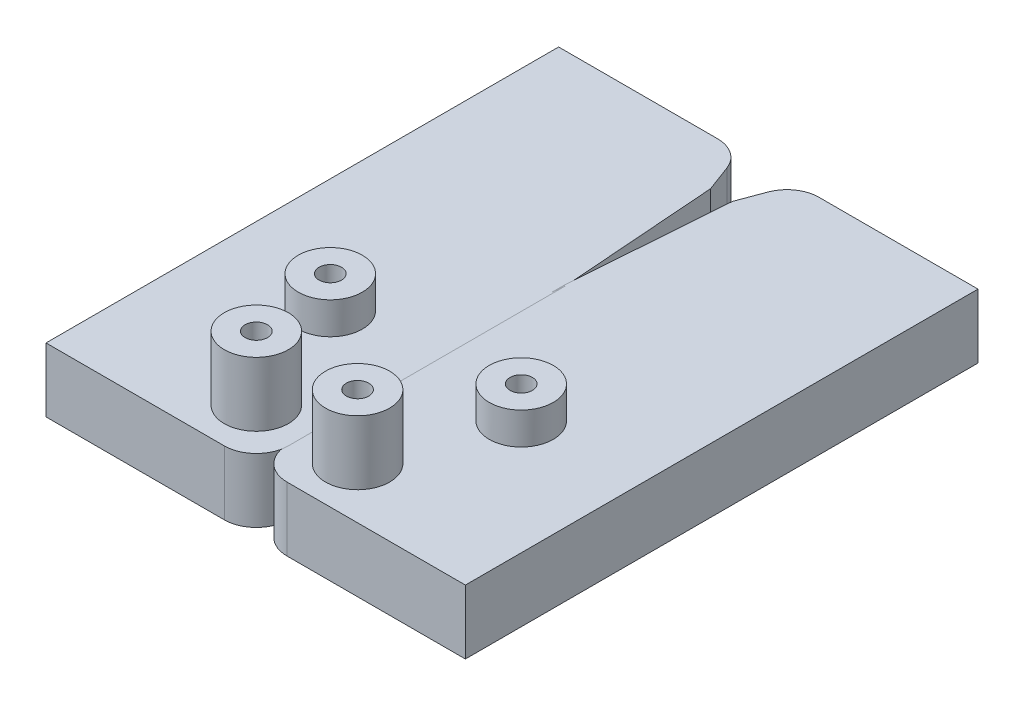
SolidWorks part; units mm, degrees
ref_plane "Front Plane" through (0, 0, 0) normal (0, 0, 1) x (1, 0, 0)
ref_plane "Top Plane" through (0, 0, 0) normal (0, 1, 0) x (1, 0, 0)
ref_plane "Right Plane" through (0, 0, 0) normal (1, 0, 0) x (0, 0, -1)
sketch "Sketch1" plane through (0, 0, 0) normal (0, 1, 0) x (1, 0, 0)
  line L0 (-32.7242, 27.6175) -> (-7.9076, 27.6175)
  line L1 (-3.2221, 24.3628) -> (-1.7139, 20.314)
  line L2 (-1.7139, 20.314) -> (0.1, -4.0497)
  line L3 (0.1, -4.0497) -> (0.1, -47.3825)
  line L4 (-4.9, -52.3825) -> (-32.7242, -52.3825)
  line L5 (-32.7242, -52.3825) -> (-32.7242, 27.6175)
  arc A0 (-7.9076, 27.6175) -> (-3.2221, 24.3628) centre (-7.9076, 22.6175) cw
  arc A1 (0.1, -47.3825) -> (-4.9, -52.3825) centre (-4.9, -47.3825) cw
  dimension "D2" = 5
  dimension "D1" = 80
  dimension "D3" = 0.1
extrude "Boss-Extrude1" add sketch "Sketch1" along normal blind 10
sketch "Sketch2" plane through (0, 10, 0) normal (0, 1, 0) x (1, 0, 0)
  line L0 (0.1, -47.3825) -> (0.1, -4.0497) construction
  line L1 (-32.7242, -52.3825) -> (-4.9, -52.3825) construction
  circle A0 centre (-7.9, -44.3825) radius 5
  dimension "D1" = 8
  dimension "D2" = 8
extrude "Boss-Extrude2" add sketch "Sketch2" along normal blind 10
sketch "Sketch3" plane through (0, 10, 0) normal (0, 1, 0) x (1, 0, 0)
  line L0 (0.1, -47.3825) -> (0.1, -4.0497) construction
  circle A0 centre (-14.9, -25.8407) radius 5
  dimension "D1" = 15
extrude "Boss-Extrude3" add sketch "Sketch3" along normal blind 5
sketch "Sketch4" plane through (0, 20, 0) normal (0, 1, 0) x (1, 0, 0)
  circle A0 centre (-7.9, -44.3825) radius 1.75
extrude "Cut-Extrude1" cut sketch "Sketch4" against normal blind 10
sketch "Sketch5" plane through (0, 15, 0) normal (0, 1, 0) x (1, 0, 0)
  circle A0 centre (-14.9, -25.8407) radius 1.75
extrude "Cut-Extrude2" cut sketch "Sketch5" against normal blind 10
mirror "Mirror4" about plane through (0, 0, 0) normal (1, 0, 0) of bodies 105
